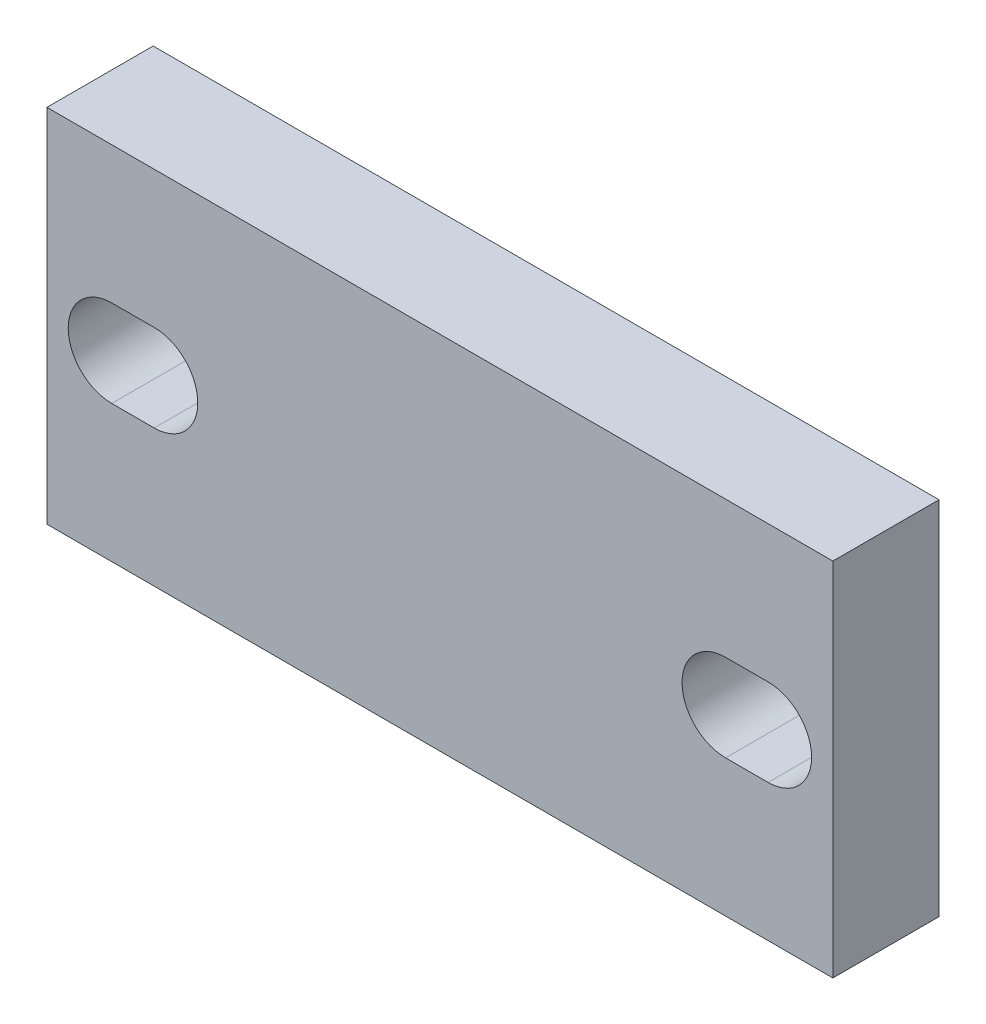
SolidWorks part; units mm, degrees
ref_plane "Front Plane" through (0, 0, 0) normal (0, 0, 1) x (1, 0, 0)
ref_plane "Top Plane" through (0, 0, 0) normal (0, 1, 0) x (1, 0, 0)
ref_plane "Right Plane" through (0, 0, 0) normal (1, 0, 0) x (0, 0, -1)
sketch "Sketch1" plane through (0, 0, 0) normal (0, 0, 1) x (1, 0, 0)
  line L0 (-14.45, 0) -> (14.45, 0) construction
  line L1 (-18.5, -8.5) -> (18.5, -8.5)
  line L2 (-18.5, -8.5) -> (-18.5, 8.5)
  line L3 (-18.5, 8.5) -> (18.5, 8.5)
  line L4 (18.5, -8.5) -> (18.5, 8.5)
  line L5 (-18.5, -8.5) -> (18.5, 8.5) construction
  line L6 (-18.5, 8.5) -> (18.5, -8.5) construction
  line L7 (-12.4, 4.7773) -> (12.4, 4.7773) construction
  line L8 (-15.45, 0) -> (-13.45, 0) construction
  line L9 (-15.45, 2.05) -> (-13.45, 2.05)
  line L10 (-15.45, -2.05) -> (-13.45, -2.05)
  line L11 (0, -8.5) -> (0, 0) construction
  line L12 (15.45, 0) -> (13.45, 0) construction
  line L13 (15.45, 2.05) -> (13.45, 2.05)
  line L14 (15.45, -2.05) -> (13.45, -2.05)
  circle A0 centre (-14.45, 0) radius 2.05 construction
  circle A1 centre (14.45, 0) radius 2.05 construction
  arc A2 (-15.45, 2.05) -> (-15.45, -2.05) centre (-15.45, 0) ccw
  arc A3 (-13.45, -2.05) -> (-13.45, 2.05) centre (-13.45, 0) ccw
  arc A4 (15.45, 2.05) -> (15.45, -2.05) centre (15.45, 0) cw
  arc A5 (13.45, -2.05) -> (13.45, 2.05) centre (13.45, 0) cw
  point P0 (0, 0)
  point P10 (-12.4, 0)
  point P12 (12.4, 0)
  point P14 (-16.5, 0)
  point P17 (-14.45, 0)
  point P24 (14.45, 0)
  dimension "D4" = 4.1
  dimension "D1" = 17
  dimension "D2" = 2
  dimension "D3" = 1
  dimension "D5" = 24.8
extrude "Boss-Extrude1" add sketch "Sketch1" along normal blind 5
